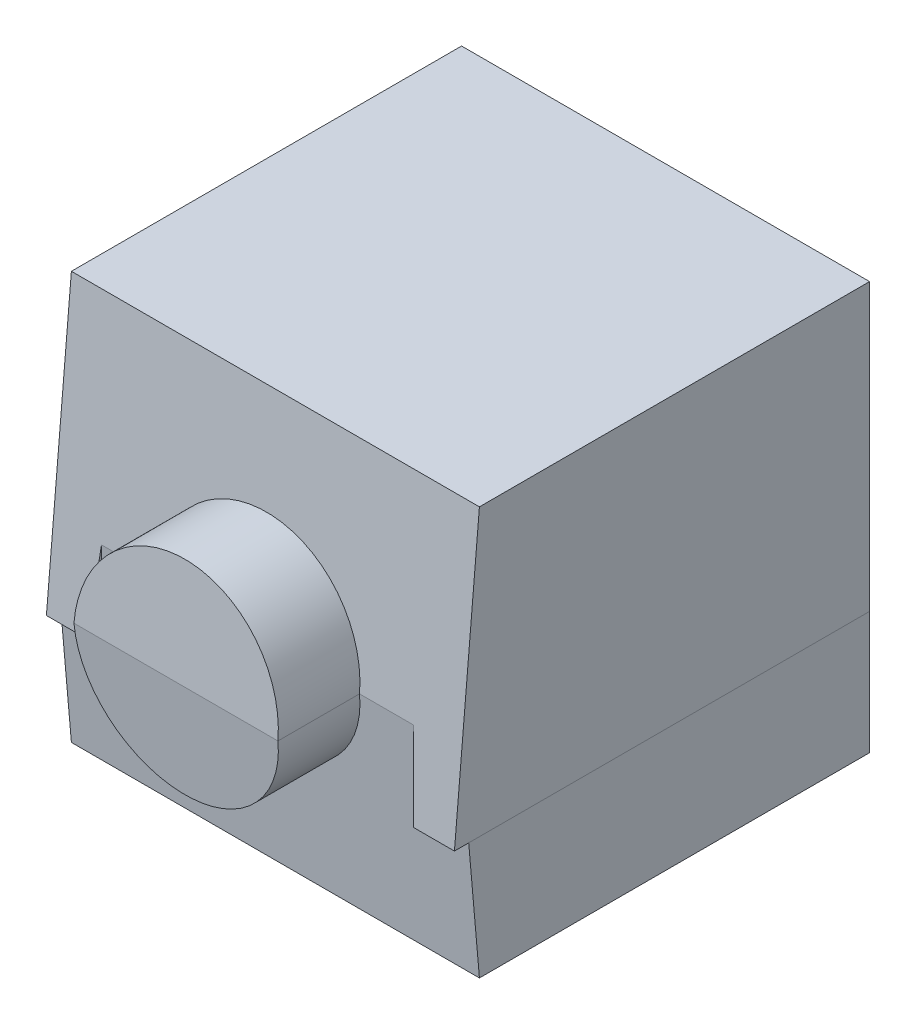
SolidWorks part; units mm, degrees
ref_plane "Ebene vorne" through (0, 0, 0) normal (0, 0, 1) x (1, 0, 0)
ref_plane "Ebene oben" through (0, 0, 0) normal (0, 1, 0) x (1, 0, 0)
ref_plane "Ebene rechts" through (0, 0, 0) normal (1, 0, 0) x (0, 0, -1)
sketch "Skizze1" plane through (0, 0, 0) normal (0, 1, 0) x (1, 0, 0)
  line L0 (0, 0) -> (0, -33366.4239) construction
  line L1 (0, 0) -> (33366.4239, 0) construction
  line L3 (-5, 5) -> (5, 5)
  line L4 (-5, 5) -> (-5, -5)
  line L5 (-5, -5) -> (5, -5)
  line L6 (5, 5) -> (5, -5)
  dimension "D1" = 10
extrude "Aufsatz-Linear austragen1" add sketch "Skizze1" along normal mid plane 10
sketch "Skizze2" plane through (0, 0, 5) normal (0, 0, 1) x (1, 0, 0)
  circle A0 centre (0, 0) radius 2.5
  dimension "D1" = 5
extrude "Aufsatz-Linear austragen2" add sketch "Skizze2" along normal blind 2
sketch "Skizze3" plane through (0, 0, 5) normal (0, 0, 1) x (1, 0, 0)
  line L0 (-5, -2) -> (-4, -2)
  line L1 (-5, 5) -> (-5, -5) construction
  line L2 (-4, -2) -> (-3.825, 0)
  line L3 (-3.825, 0) -> (3.825, 0)
  line L5 (-5, -5) -> (5, -5) construction
  line L6 (0, 0) -> (0, -50000) construction
  line L7 (4, -2) -> (3.825, 0)
  line L8 (5, -2) -> (4, -2)
  point P14 (0, 0)
  dimension "D1" = 8
  dimension "D2" = 3
  dimension "D3" = 5
split "Abspalten1" trim tools "Skizze3" bodies to split 102 resulting bodies 105 106
draft "Formschräge5" type of draft neutral plane draft angle 5 faces to draft 2 face at (0, 1.25, 7) face at (0, 0.45, 5) neutral plane through (-3.825, 0, -5.01) neutral plane normal (0, -1, 0) reverse direction yes parameters "D1"=5
draft "Formschräge6" type of draft neutral plane draft angle 5 faces to draft 2 face at (0, -2.05, 5) face at (0, -1.25, 7) neutral plane through (-3.825, 0, -5.01) neutral plane normal (0, 1, 0) reverse direction yes parameters "D1"=5
